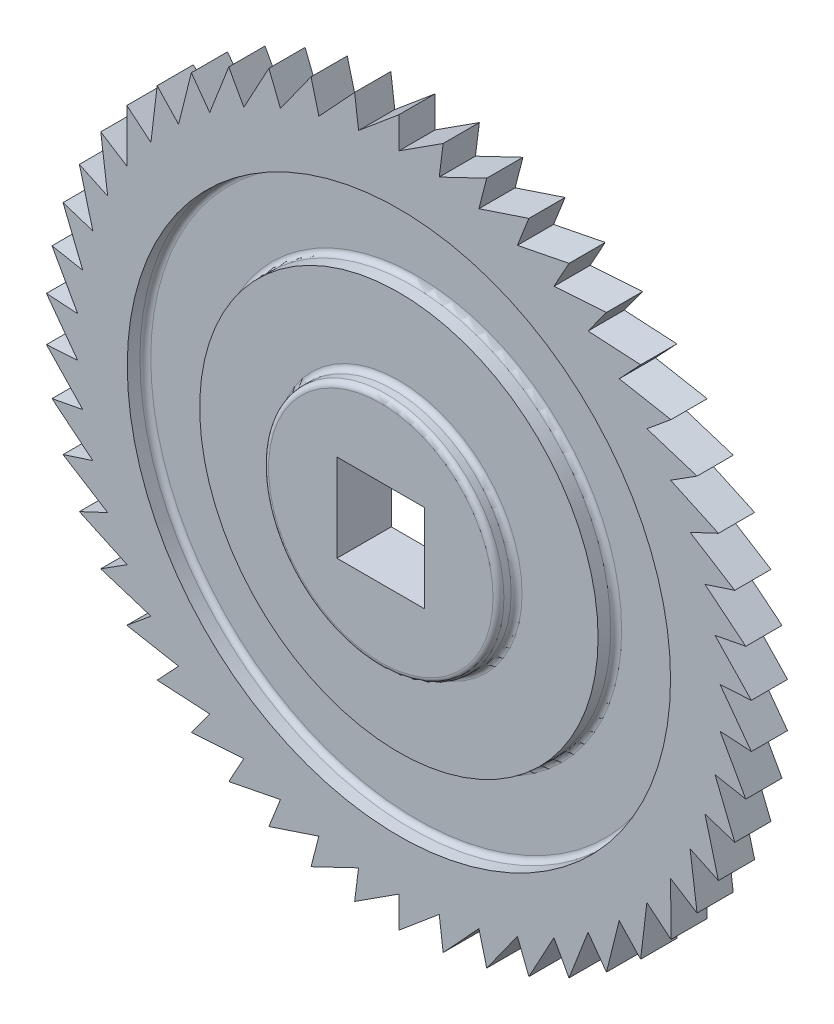
SolidWorks part; units mm, degrees
ref_plane "Front Plane" through (0, 0, 0) normal (0, 0, 1) x (1, 0, 0)
ref_plane "Top Plane" through (0, 0, 0) normal (0, 1, 0) x (1, 0, 0)
ref_plane "Right Plane" through (0, 0, 0) normal (1, 0, 0) x (0, 0, -1)
sketch "Sketch1" plane through (0, 0, 0) normal (0, 0, 1) x (1, 0, 0)
  line L1 (2.1213, -106.3787) -> (-2.1213, -106.3787)
  line L2 (2.1213, -106.3787) -> (2.1213, -110.6213)
  line L3 (2.1213, -110.6213) -> (-2.1213, -110.6213)
  line L4 (-2.1213, -106.3787) -> (-2.1213, -110.6213)
  line L5 (2.1213, -106.3787) -> (-2.1213, -110.6213) construction
  line L6 (2.1213, -110.6213) -> (-2.1213, -106.3787) construction
  circle A0 centre (0, -108.5) radius 3 construction
  circle A1 centre (0, -108.5) radius 17.5
  point P0 (0, -108.5)
  dimension "D1" = 35
sketch "Sketch2" plane through (0, 0, 0) normal (0, 0, 1) x (1, 0, 0)
  line L0 (0, -91) -> (0, -89)
  line L1 (0, -89) -> (-2.6182, -91.197)
  circle A0 centre (0, -108.5) radius 17.5 construction
  arc A1 (-2.6182, -91.197) -> (0, -91) centre (0, -108.5) ccw
  dimension "D1" = 50
  dimension "D2" = 2
extrude "Boss-Extrude1" add sketch "Sketch2" against normal up to vertex (2 mm away)
pattern_circular "CirPattern1" count 50 over 360 about axis through (0, -108.5, 0) along (0, 0, 1) of "Boss-Extrude1"
sketch "Sketch3" plane through (0, 0, 0) normal (0, 0, 1) x (1, 0, 0)
  line L0 (2.1213, -106.3787) -> (2.1213, -110.6213) construction
  line L1 (2.1213, -110.6213) -> (-2.1213, -110.6213) construction
  line L2 (-2.1213, -106.3787) -> (-2.1213, -110.6213) construction
  line L3 (2.1213, -106.3787) -> (-2.1213, -106.3787) construction
  line L4 (2.1213, -106.3787) -> (2.1213, -110.6213) construction
  line L5 (2.1213, -110.6213) -> (-2.1213, -110.6213) construction
  line L6 (-2.1213, -106.3787) -> (-2.1213, -110.6213) construction
  line L7 (2.1213, -106.3787) -> (-2.1213, -106.3787) construction
  line L8 (-2.4213, -106.0787) -> (-2.4213, -110.9213)
  line L9 (2.4213, -110.9213) -> (-2.4213, -110.9213)
  line L10 (2.4213, -106.0787) -> (2.4213, -110.9213)
  line L11 (2.4213, -106.0787) -> (-2.4213, -106.0787)
  dimension "D1" = 0.3
extrude "Cut-Extrude2" cut sketch "Sketch3" against normal through all
sketch "Sketch4" plane through (0, 0, 0) normal (0, 0, 1) x (1, 0, 0)
  circle A0 centre (0, -108.5) radius 11
  circle A1 centre (0, -108.5) radius 15
  dimension "D1" = 22
  dimension "D2" = 30
extrude "Cut-Extrude3" cut sketch "Sketch4" against normal blind 1
sketch "Sketch5" plane through (0, 0, 0) normal (0, 0, 1) x (1, 0, 0)
  line L5 (2.4213, -106.0787) -> (-2.4213, -106.0787)
  line L6 (2.4213, -110.9213) -> (2.4213, -106.0787)
  line L7 (-2.4213, -110.9213) -> (2.4213, -110.9213)
  line L8 (-2.4213, -106.0787) -> (-2.4213, -110.9213)
  line L9 (2.4213, -106.0787) -> (-2.4213, -106.0787)
  line L10 (2.4213, -110.9213) -> (2.4213, -106.0787)
  line L11 (-2.4213, -110.9213) -> (2.4213, -110.9213)
  line L12 (-2.4213, -106.0787) -> (-2.4213, -110.9213)
  circle A0 centre (0, -108.5) radius 6.5
  dimension "D1" = 13
  dimension "D2" = 0
extrude "Boss-Extrude2" add sketch "Sketch5" along normal blind 1
fillet "Fillet1" radius 0.3 4 edges at (15, -108.5, -1) (11, -108.5, -1) (6.5, -108.5, 1) (6.5, -108.5, 0)
